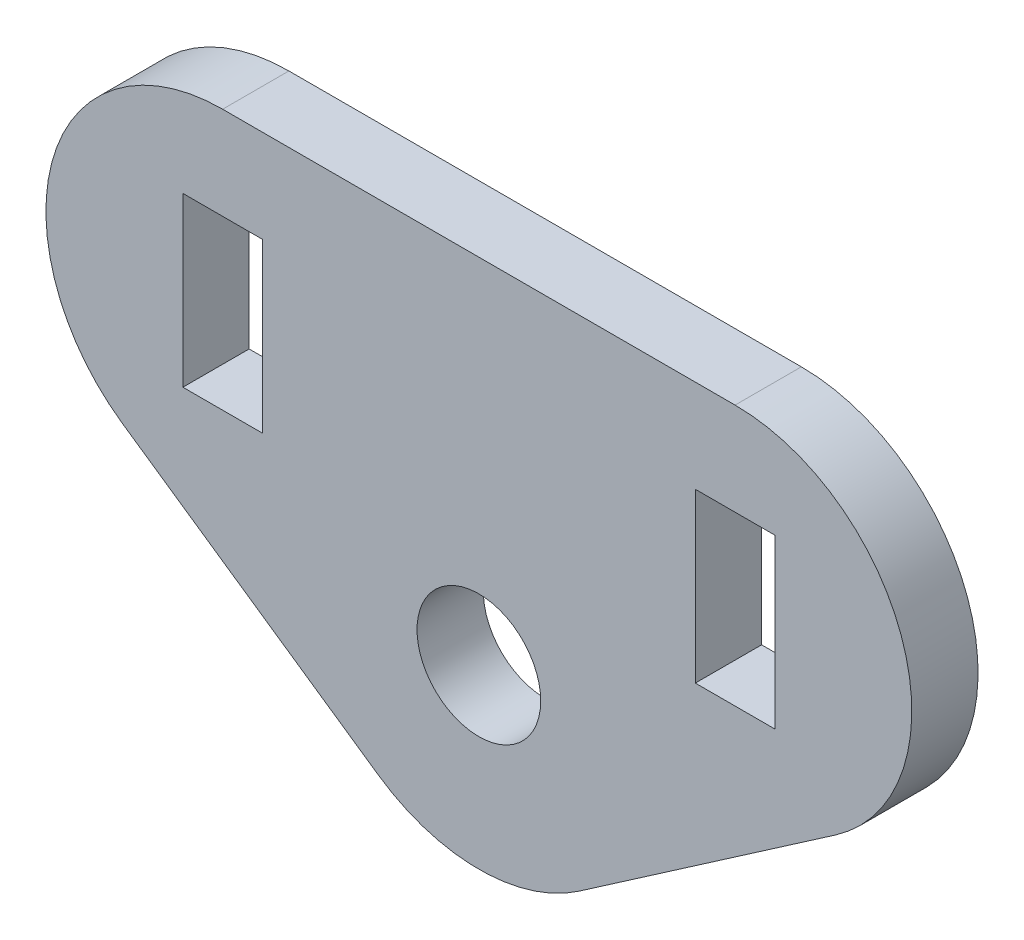
SolidWorks part; units mm, degrees
ref_plane "Front" through (0, 0, 0) normal (0, 0, 1) x (1, 0, 0)
ref_plane "Top" through (0, 0, 0) normal (0, 1, 0) x (1, 0, 0)
ref_plane "Right" through (0, 0, 0) normal (1, 0, 0) x (0, 0, -1)
sketch "Sketch1" plane through (0, 0, 0) normal (0, 0, 1) x (1, 0, 0)
  line L0 (0, 0) -> (58, 40) construction
  line L1 (58, 40) -> (-58, 40) construction
  line L2 (-58, 40) -> (0, 0) construction
  line L3 (186.4557, 80) -> (-186.4557, 80)
  line L4 (-186.4557, 80) -> (0, -48.5901)
  line L5 (0, -48.5901) -> (186.4557, 80)
  line L7 (-67, 21) -> (-49, 21)
  line L8 (-67, 21) -> (-67, 59)
  line L9 (-67, 59) -> (-49, 59)
  line L10 (-49, 21) -> (-49, 59)
  line L11 (-67, 21) -> (-49, 59) construction
  line L12 (-67, 59) -> (-49, 21) construction
  line L13 (49, 21) -> (67, 21)
  line L14 (49, 21) -> (49, 59)
  line L15 (49, 59) -> (67, 59)
  line L16 (67, 21) -> (67, 59)
  line L17 (49, 21) -> (67, 59) construction
  line L18 (49, 59) -> (67, 21) construction
  circle A0 centre (0, 0) radius 14
  point P7 (0, 40)
  dimension "D1" = 18
  dimension "D2" = 38
  dimension "D8" = 28
  dimension "D3" = 40
  dimension "D4" = 116
  dimension "D6" = 18
  dimension "D7" = 38
  dimension "D5" = 40
extrude "Boss-Extrude1" add sketch "Sketch1" along normal blind 15
fillet "Fillet1" radius 40 3 edges at (0, -48.5901, 7.5) (-186.4557, 80, 7.5) (186.4557, 80, 7.5)
sketch "Sketch2" plane through (0, 0, 15) normal (0, 0, 1) x (1, 0, 0)
  line L1 (-64, -14.3912) -> (-66, -14.3912)
  line L2 (-64, -14.3912) -> (-64, 54.3912)
  line L3 (-64, 54.3912) -> (-66, 54.3912)
  line L4 (-66, -14.3912) -> (-66, 54.3912)
  line L5 (-64, -14.3912) -> (-66, 54.3912) construction
  line L6 (-64, 54.3912) -> (-66, -14.3912) construction
  line L7 (66, -14.3912) -> (64, -14.3912)
  line L8 (66, -14.3912) -> (66, 54.3912)
  line L9 (66, 54.3912) -> (64, 54.3912)
  line L10 (64, -14.3912) -> (64, 54.3912)
  line L11 (66, -14.3912) -> (64, 54.3912) construction
  line L12 (66, 54.3912) -> (64, -14.3912) construction
  point P0 (-65, 20)
  point P7 (65, 20)
  dimension "D1" = 2
  dimension "D2" = 2
extrude "Cut-Extrude1" [suppressed] cut sketch "Sketch2" against normal through all
